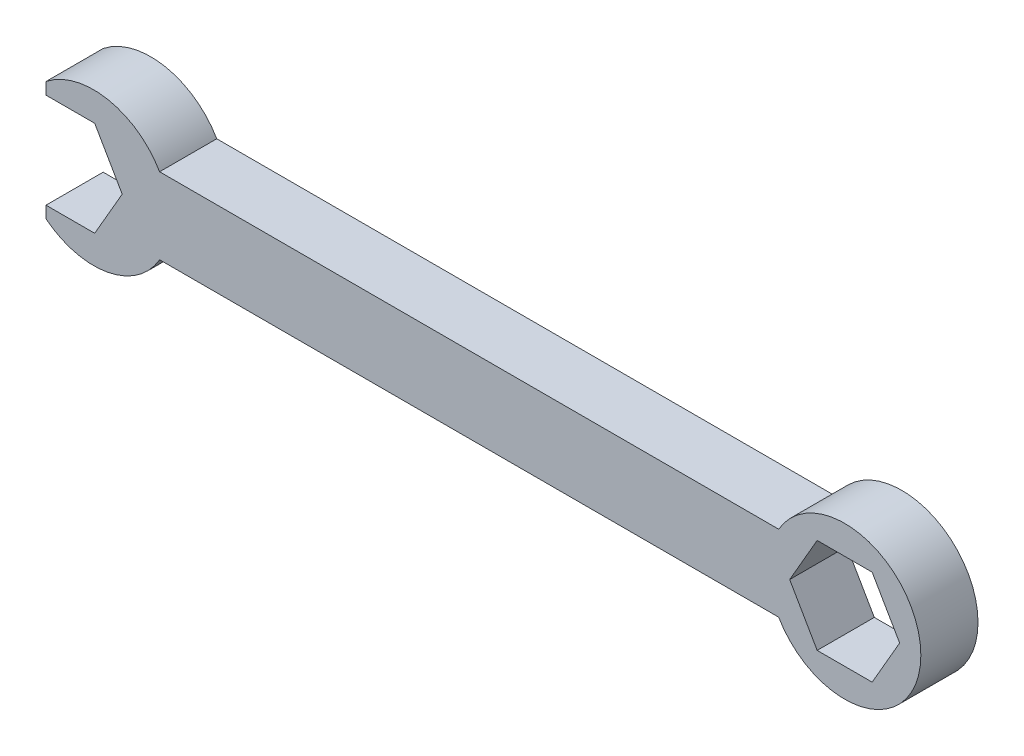
SolidWorks part; units mm, degrees
material "Cast Alloy Steel"
ref_plane "Front Plane" through (0, 0, 0) normal (0, 0, 1) x (1, 0, 0)
ref_plane "Top Plane" through (0, 0, 0) normal (0, 1, 0) x (1, 0, 0)
ref_plane "Right Plane" through (0, 0, 0) normal (1, 0, 0) x (0, 0, -1)
sketch "Sketch3" plane through (0, 0, 0) normal (0, 0, 1) x (1, 0, 0)
  line L0 (0, 0) -> (-103.67, 0) construction
  line L1 (-8.7988, 5.08) -> (-91.3488, 5.08)
  line L2 (7.3323, 0) -> (3.6662, 6.35)
  line L3 (3.6662, 6.35) -> (-3.6662, 6.35)
  line L4 (-3.6662, 6.35) -> (-7.3323, 0)
  line L5 (-7.3323, 0) -> (-3.6662, -6.35)
  line L6 (-3.6662, -6.35) -> (3.6662, -6.35)
  line L7 (3.6662, -6.35) -> (7.3323, 0)
  line L8 (-106.4976, 7.9311) -> (-106.4976, 6.35)
  line L9 (-96.3376, 0) -> (-100.0038, 6.35)
  line L10 (-100.0038, 6.35) -> (-106.4976, 6.35)
  line L13 (-106.4976, -6.35) -> (-100.0038, -6.35)
  line L14 (-100.0038, -6.35) -> (-96.3376, 0)
  line L15 (-91.3488, -5.08) -> (-8.7988, -5.08)
  line L16 (-109.1692, 3.175) -> (-111.0023, 0) [skipped]
  line L17 (-109.1692, -3.175) -> (-107.3362, -6.35) [skipped]
  line L18 (-106.4976, -6.35) -> (-106.4976, -7.9311)
  line L19 (-106.4976, -6.35) -> (-100.0038, -6.35)
  line L20 (-7.3323, 0) -> (-3.6662, 6.35)
  line L21 (3.6662, 6.35) -> (7.3323, 0)
  line L22 (3.6662, -6.35) -> (-3.6662, -6.35)
  arc A1 (-8.7988, -5.08) -> (-8.7988, 5.08) centre (0, 0) ccw
  arc A3 (-91.3488, 5.08) -> (-106.4976, 7.9311) centre (-100.1476, 0) ccw
  arc A4 (-106.4976, -7.9311) -> (-91.3488, -5.08) centre (-100.1476, 0) ccw
  point P10 (0, 0)
  dimension "D2" = 20.32
  dimension "D5" = 20.32
  dimension "D1" = 12.7
  dimension "D3" = 5.08
  dimension "D4" = 82.55
  dimension "D6" = 12.7
  dimension "D7" = 6.4938
  dimension "D8" = 6.35
  dimension "D9" = 5.08
extrude "Boss-Extrude1" add sketch "Sketch3" along normal blind 7.62
